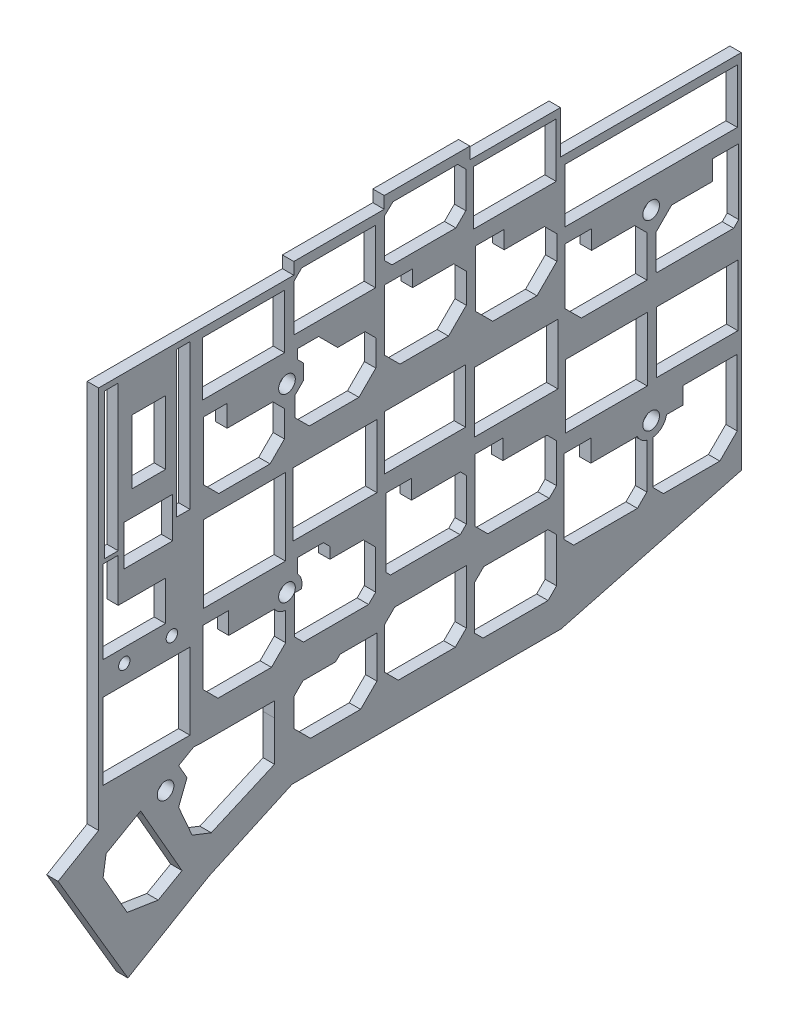
SolidWorks part; units mm, degrees
ref_plane "Спереди" through (0, 0, 0) normal (0, 0, 1) x (1, 0, 0)
ref_plane "Сверху" through (0, 0, 0) normal (0, 1, 0) x (1, 0, 0)
ref_plane "Справа" through (0, 0, 0) normal (1, 0, 0) x (0, 0, -1)
sketch "Эскиз1" plane through (0, 0, 0) normal (1, 0, 0) x (0, 0, -1)
  line L0 (0, 0) -> (0, -80.5)
  line L2 (41, 2.5) -> (41, 0)
  line L3 (41, 0) -> (0, 0)
  line L4 (41, 2.5) -> (60, 2.5)
  line L5 (60, 2.5) -> (60, 5)
  line L6 (41.1751, -59.6669) -> (41.1751, -57.8712)
  line L7 (41.1751, -57.8712) -> (42.5834, -57.8712)
  line L9 (78, 5) -> (78, 2.5)
  line L10 (78, 2.5) -> (97, 2.5)
  line L11 (97, 2.5) -> (97, -6.5)
  line L12 (97, -6.5) -> (135, -6.5)
  line L13 (135, -6.5) -> (135, -82.5)
  line L14 (135, -82.5) -> (97.1532, -92.4105)
  line L15 (97.1532, -92.4105) -> (40.6532, -92.4105)
  line L16 (40.6532, -92.4105) -> (23.1532, -100.4105)
  line L17 (23.1532, -100.4105) -> (6.1532, -110.4105)
  line L18 (6.1532, -110.4105) -> (-8.5, -85.5)
  line L19 (-8.5, -85.5) -> (0, -80.5)
  line L20 (115.2444, -43.8669) -> (98.0747, -43.8669)
  line L21 (134.2812, -43.8669) -> (117.1398, -43.8669)
  line L22 (134.2812, -43.8669) -> (134.2812, -56.7301)
  line L23 (134.2812, -56.7301) -> (117.1398, -56.7301)
  line L24 (117.1398, -43.8669) -> (117.1398, -56.7301)
  line L25 (134.2812, -43.8669) -> (117.1398, -56.7301) construction
  line L26 (134.2812, -56.7301) -> (117.1398, -43.8669) construction
  line L27 (115.2444, -43.8669) -> (115.2444, -57.2681)
  line L28 (115.2444, -57.2681) -> (98.0747, -57.2681)
  line L29 (98.0747, -43.8669) -> (98.0747, -57.2681)
  line L30 (96.4817, -35.7366) -> (78.9435, -35.7366)
  line L31 (96.4817, -35.7366) -> (96.4817, -48.4214)
  line L32 (96.4817, -48.4214) -> (78.9435, -48.4214)
  line L33 (78.9435, -35.7366) -> (78.9435, -48.4214)
  line L34 (77.0753, -34.3134) -> (60.0344, -34.3134)
  line L35 (77.0753, -34.3134) -> (77.0753, -45.6876)
  line L36 (77.0753, -45.6876) -> (60.0344, -45.6876)
  line L37 (60.0344, -34.3134) -> (60.0344, -45.6876)
  line L38 (39.2504, -34.986) -> (22.0882, -34.986)
  line L39 (39.2504, -34.986) -> (39.2504, -51.1261)
  line L40 (39.2504, -51.1261) -> (22.0882, -51.1261)
  line L41 (22.0882, -34.986) -> (22.0882, -51.1261)
  line L42 (58.4588, -34.9591) -> (40.7884, -34.9591)
  line L43 (58.4588, -34.9591) -> (58.4588, -48.279)
  line L44 (58.4588, -48.279) -> (40.7884, -48.279)
  line L45 (40.7884, -34.9591) -> (40.7884, -48.279)
  line L46 (39.085, -1.7522) -> (21.8397, -1.7522)
  line L47 (39.085, -1.7522) -> (39.085, -13.1264)
  line L48 (39.085, -13.1264) -> (21.8397, -13.1264)
  line L49 (21.8397, -1.7522) -> (21.8397, -13.1264)
  line L50 (114.4249, -8.3173) -> (97.9345, -8.3173)
  line L52 (115.1819, -19.6916) -> (97.9345, -19.6916)
  line L53 (97.9345, -8.3173) -> (97.9345, -19.6916)
  line L54 (75.4231, 2.9496) -> (61.8402, 2.9496)
  line L55 (77.1401, 1.2326) -> (77.1401, -6.3324)
  line L56 (75.0478, -8.4247) -> (61.6231, -8.4247)
  line L57 (60.0575, 1.2815) -> (60.0575, -6.8591)
  line L58 (58.1743, 0.5012) -> (42.6577, 0.5012)
  line L59 (58.1743, 0.5012) -> (58.1743, -10.8731)
  line L60 (58.1743, -10.8731) -> (41.0138, -10.8731)
  line L61 (41.0138, -1.1427) -> (41.0138, -10.8731)
  line L62 (134.1721, -8.3173) -> (114.4249, -8.3173)
  line L63 (134.1721, -8.3173) -> (134.1721, -19.6916)
  line L64 (134.1721, -19.6916) -> (115.1819, -19.6916)
  line L66 (96.1243, 0.8798) -> (78.7359, 0.8798)
  line L67 (96.1243, 0.8798) -> (96.1243, -10.4945)
  line L68 (96.1243, -10.4945) -> (78.7359, -10.4945)
  line L69 (78.7359, 0.8798) -> (78.7359, -10.4945)
  line L70 (61.8402, 2.9496) -> (60.0575, 1.2815)
  line L71 (78, 5) -> (60, 5)
  line L72 (75.4231, 2.9496) -> (77.1401, 1.2326)
  line L73 (77.1401, -6.3324) -> (75.0478, -8.4247)
  line L74 (60.0575, -6.8591) -> (61.6231, -8.4247)
  line L75 (42.6577, 0.5012) -> (41.0138, -1.1427)
  line L76 (134.4455, -22.7884) -> (134.4455, -36.6029)
  line L81 (19.1956, -1.1776) -> (16.3872, -1.1776)
  line L82 (19.1956, -1.1776) -> (19.1956, -31.6801)
  line L83 (19.1956, -31.6801) -> (16.3872, -31.6801)
  line L84 (16.3872, -1.1776) -> (16.3872, -31.6801)
  line L85 (14.07, -8.4247) -> (7.0177, -8.4247)
  line L86 (14.07, -8.4247) -> (14.07, -21.8565)
  line L87 (14.07, -21.8565) -> (7.0177, -21.8565)
  line L88 (7.0177, -8.4247) -> (7.0177, -21.8565)
  line L89 (4.123, -1.1776) -> (1.2335, -1.1776)
  line L90 (4.123, -1.1776) -> (4.123, -31.6801)
  line L91 (4.123, -31.6801) -> (1.2335, -31.6801)
  line L92 (1.2335, -1.1776) -> (1.2335, -31.6801)
  line L93 (15.5712, -27.119) -> (5.2984, -27.119)
  line L94 (15.5712, -27.119) -> (15.5712, -35.5999)
  line L95 (15.5712, -35.5999) -> (5.2984, -35.5999)
  line L96 (5.2984, -27.119) -> (5.2984, -35.5999)
  line L97 (4.123, -32.4925) -> (0.9179, -32.4925)
  line L98 (4.123, -32.4925) -> (4.123, -41.6217)
  line L100 (0.9179, -32.4925) -> (0.9179, -49.8922)
  line L105 (134.4455, -36.6029) -> (133.3973, -37.6511)
  line L106 (133.3973, -37.6511) -> (117.3195, -37.6511)
  line L107 (117.3195, -37.6511) -> (117.0331, -37.3648)
  line L108 (117.0331, -37.3648) -> (117.0331, -30.2531)
  line L109 (117.0331, -30.2531) -> (120.3714, -26.9148)
  line L110 (120.3714, -26.9148) -> (128.9098, -26.9148)
  line L111 (128.9098, -26.9148) -> (128.9098, -22.7884)
  line L112 (128.9098, -22.7884) -> (134.4455, -22.7884)
  line L113 (97.9345, -22.7884) -> (97.9345, -34.5253)
  line L114 (97.9345, -34.5253) -> (101.3903, -37.9811)
  line L115 (101.3903, -37.9811) -> (115.1819, -37.9811)
  line L116 (115.1819, -37.9811) -> (115.1819, -29.341)
  line L117 (115.1819, -29.341) -> (112.6062, -26.7653)
  line L118 (112.6062, -26.7653) -> (103.5391, -26.7653)
  line L119 (103.5391, -26.7653) -> (103.5391, -22.7884)
  line L120 (103.5391, -22.7884) -> (97.9345, -22.7884)
  line L121 (79.1801, -13.7463) -> (79.1801, -25.658)
  line L122 (79.1801, -25.658) -> (82.7928, -29.2707)
  line L123 (82.7928, -29.2707) -> (92.0789, -29.2707)
  line L124 (92.0789, -29.2707) -> (96.2546, -25.095)
  line L125 (96.2546, -25.095) -> (96.2546, -20.0763)
  line L126 (96.2546, -20.0763) -> (93.6526, -17.4743)
  line L127 (93.6526, -17.4743) -> (85.1909, -17.4743)
  line L128 (85.1909, -17.4743) -> (85.1909, -13.7463)
  line L129 (85.1909, -13.7463) -> (79.1801, -13.7463)
  line L130 (60.0575, -11.5433) -> (60.0575, -24.0649)
  line L131 (60.0575, -24.0649) -> (63.3126, -27.32)
  line L132 (63.3126, -27.32) -> (73.507, -27.32)
  line L133 (73.507, -27.32) -> (77.2434, -23.5835)
  line L134 (77.2434, -23.5835) -> (77.2434, -17.384)
  line L135 (77.2434, -17.384) -> (74.5983, -14.7389)
  line L136 (74.5983, -14.7389) -> (65.9509, -14.7389)
  line L137 (65.9509, -14.7389) -> (65.9509, -11.2966)
  line L138 (65.9509, -11.2966) -> (60.0575, -11.2966)
  line L139 (60.0575, -11.2966) -> (60.0575, -11.5433)
  line L140 (41.2039, -21.9909) -> (41.2039, -25.9973)
  line L141 (41.2039, -25.9973) -> (44.2553, -29.0487)
  line L142 (44.2553, -29.0487) -> (54.6792, -29.0487)
  line L143 (54.6792, -29.0487) -> (58.222, -25.506)
  line L144 (58.222, -25.506) -> (58.222, -19.9911)
  line L145 (58.222, -19.9911) -> (55.979, -17.7482)
  line L146 (55.979, -17.7482) -> (50.2068, -17.7482)
  line L147 (50.2068, -17.7482) -> (46.2049, -13.7463)
  line L148 (46.2049, -13.7463) -> (41.7463, -13.7463)
  line L149 (41.7463, -13.7463) -> (41.7463, -15.6937)
  line L150 (41.7463, -15.6937) -> (43.0018, -16.9493)
  line L151 (43.0018, -16.9493) -> (43.0018, -20.193)
  line L152 (43.0018, -20.193) -> (41.2039, -21.9909)
  line L153 (22.0882, -16.2929) -> (22.0882, -28.227)
  line L154 (22.0882, -16.2929) -> (27.0021, -16.2929)
  line L155 (27.0021, -16.2929) -> (27.0021, -20.8389)
  line L156 (27.0021, -20.8389) -> (36.6084, -20.8389)
  line L157 (36.6084, -20.8389) -> (39.04, -23.2705)
  line L158 (39.04, -23.2705) -> (39.04, -28.8092)
  line L159 (39.04, -28.8092) -> (36.0163, -31.8329)
  line L160 (36.0163, -31.8329) -> (25.2427, -31.8329)
  line L161 (25.2427, -31.8329) -> (22.0882, -28.6784)
  line L162 (22.0882, -28.6784) -> (22.0882, -28.227)
  line L163 (134.1429, -60.9376) -> (134.1429, -74.9003)
  line L164 (134.1429, -74.9003) -> (130.4912, -78.552)
  line L165 (130.4912, -78.552) -> (118.6526, -78.552)
  line L166 (118.6526, -78.552) -> (116.4367, -76.3361)
  line L167 (116.4367, -76.3361) -> (116.4367, -67.1958)
  line L169 (119.2828, -64.5018) -> (122.7046, -64.5018)
  line L170 (122.7046, -64.5018) -> (122.7046, -60.9376)
  line L171 (122.7046, -60.9376) -> (134.1429, -60.9376)
  line L172 (115.1516, -67.0844) -> (115.1516, -76.5165)
  line L173 (115.1516, -76.5165) -> (113.175, -78.4931)
  line L174 (113.175, -78.4931) -> (99.8049, -78.4931)
  line L175 (99.8049, -78.4931) -> (97.7485, -76.4366)
  line L176 (97.7485, -76.4366) -> (97.7485, -60.8193)
  line L177 (97.7485, -60.8193) -> (103.3958, -60.8193)
  line L178 (103.3958, -60.8193) -> (103.3958, -65.3906)
  line L179 (103.3958, -65.3906) -> (113.1434, -65.3906)
  line L181 (94.3901, -72.9633) -> (96.1915, -74.7647)
  line L182 (96.1915, -74.7647) -> (96.1915, -84.0984)
  line L183 (96.1915, -84.0984) -> (94.4093, -85.8807)
  line L184 (94.4093, -85.8807) -> (80.7614, -85.8807)
  line L185 (80.7614, -85.8807) -> (78.9435, -84.0628)
  line L186 (78.9435, -84.0628) -> (78.9435, -74.9072)
  line L187 (78.9435, -74.9072) -> (80.9028, -72.9479)
  line L188 (80.9028, -72.9479) -> (89.3287, -72.9479)
  line L189 (89.3287, -72.9479) -> (89.3072, -72.9633)
  line L190 (89.3072, -72.9633) -> (92.0789, -72.9633)
  line L191 (92.0789, -72.9633) -> (94.3901, -72.9633)
  line L192 (96.1915, -57.6954) -> (96.1915, -63.958)
  line L193 (96.1915, -57.6954) -> (94.18, -55.6839)
  line L194 (94.18, -55.6839) -> (84.911, -55.6839)
  line L195 (84.911, -55.6839) -> (84.911, -51.5792)
  line L196 (84.911, -51.5792) -> (79.0384, -51.5792)
  line L197 (79.0384, -51.5792) -> (79.0384, -64.6854)
  line L198 (79.0384, -64.6854) -> (81.7682, -67.4152)
  line L199 (81.7682, -67.4152) -> (94.6543, -67.4152)
  line L200 (94.6543, -67.4152) -> (96.1915, -65.878)
  line L201 (96.1915, -65.878) -> (96.1915, -63.958)
  line L202 (60.3332, -49.2925) -> (60.3332, -63.7083)
  line L203 (60.3332, -63.7083) -> (61.3103, -64.6854)
  line L204 (61.3103, -64.6854) -> (75.9502, -64.6854)
  line L205 (75.9502, -64.6854) -> (77.2397, -63.3959)
  line L206 (77.2397, -63.3959) -> (77.2397, -54.5235)
  line L207 (77.2397, -54.5235) -> (76.006, -53.2898)
  line L208 (76.006, -53.2898) -> (65.7297, -53.2898)
  line L209 (65.7297, -53.2898) -> (65.7297, -49.2925)
  line L210 (65.7297, -49.2925) -> (60.3332, -49.2925)
  line L211 (77.2397, -70.92) -> (77.2397, -82.3079)
  line L212 (77.2397, -82.3079) -> (74.9117, -84.6359)
  line L213 (74.9117, -84.6359) -> (62.9489, -84.6359)
  line L214 (62.9489, -84.6359) -> (60.0344, -81.7213)
  line L215 (60.0344, -81.7213) -> (60.0344, -73.1228)
  line L216 (60.0344, -73.1228) -> (62.1913, -70.966)
  line L217 (62.1913, -70.966) -> (69.6708, -70.966)
  line L218 (69.6708, -70.966) -> (69.6708, -70.92)
  line L219 (69.6708, -70.92) -> (77.2397, -70.92)
  line L220 (58.4588, -74.1904) -> (58.4588, -82.5614)
  line L221 (58.4588, -82.5614) -> (55.0335, -85.9867)
  line L222 (55.0335, -85.9867) -> (44.5165, -85.9867)
  line L223 (44.5165, -85.9867) -> (41.0138, -82.484)
  line L224 (41.0138, -82.484) -> (41.0138, -76.6283)
  line L225 (41.0138, -76.6283) -> (42.929, -74.7131)
  line L226 (42.929, -74.7131) -> (49.7913, -74.7131)
  line L227 (49.7913, -74.7131) -> (50.7049, -73.7995)
  line L228 (50.7049, -73.7995) -> (58.4588, -73.7995)
  line L229 (58.4588, -73.7995) -> (58.4588, -74.1904)
  line L230 (41.7463, -51.7434) -> (41.7463, -54.6825)
  line L234 (41.1751, -59.6669) -> (41.1751, -65.8913)
  line L235 (41.1751, -65.8913) -> (43.0301, -67.7463)
  line L236 (43.0301, -67.7463) -> (56.7142, -67.7463)
  line L237 (56.7142, -67.7463) -> (58.2067, -66.2538)
  line L238 (58.2067, -66.2538) -> (58.2067, -58.0562)
  line L239 (58.2067, -58.0562) -> (55.6211, -55.4707)
  line L240 (55.6211, -55.4707) -> (48.5878, -55.4707)
  line L241 (48.5878, -55.4707) -> (48.5878, -53.1196)
  line L242 (48.5878, -53.1196) -> (47.2116, -51.7434)
  line L243 (47.2116, -51.7434) -> (41.7463, -51.7434)
  line L244 (27.335, -54.1406) -> (27.335, -58.6932)
  line L245 (27.335, -58.6932) -> (36.9426, -58.6932)
  line L247 (39.2975, -60.0949) -> (39.2975, -65.9987)
  line L248 (39.2975, -65.9987) -> (36.3132, -68.9829)
  line L249 (36.3132, -68.9829) -> (25.0829, -68.9829)
  line L250 (25.0829, -68.9829) -> (21.9132, -65.8133)
  line L251 (21.9132, -65.8133) -> (21.9132, -54.1406)
  line L252 (21.9132, -54.1406) -> (27.335, -54.1406)
  line L253 (19.1956, -56.7301) -> (19.1956, -72.7671)
  line L254 (19.1956, -72.7671) -> (0.9179, -72.7671)
  line L255 (0.9179, -72.7671) -> (0.9179, -56.7301)
  line L256 (0.9179, -56.7301) -> (19.1956, -56.7301)
  line L258 (0.9179, -49.8922) -> (14.07, -49.8922)
  line L259 (14.07, -49.8922) -> (14.07, -41.6217)
  line L260 (14.07, -41.6217) -> (4.123, -41.6217)
  line L261 (36.9426, -75.3779) -> (36.9426, -78.5072)
  line L262 (36.9426, -78.5072) -> (36.9492, -78.5005)
  line L263 (36.9492, -78.5005) -> (36.9492, -86.9326)
  line L264 (36.9492, -86.9326) -> (23.6687, -92.7489)
  line L265 (23.6687, -92.7489) -> (19.6493, -91.1779)
  line L266 (19.6493, -91.1779) -> (16.8062, -84.6861)
  line L267 (16.8062, -84.6861) -> (18.5715, -80.1697)
  line L268 (18.5715, -80.1697) -> (16.818, -77.1037)
  line L269 (16.818, -77.1037) -> (19.9877, -75.2908)
  line L270 (36.9426, -75.3779) -> (21.3449, -75.3779)
  line L274 (9.4762, -82.4846) -> (17.528, -96.563)
  line L275 (17.528, -96.563) -> (12.5276, -99.4228)
  line L276 (12.5276, -99.4228) -> (6, -98.3963)
  line L277 (6, -98.3963) -> (0.9484, -89.5637)
  line L278 (0.9484, -89.5637) -> (1.5875, -85.5)
  line L279 (1.5875, -85.5) -> (8.8323, -81.3565)
  line L280 (8.8323, -81.3565) -> (9.4762, -82.4846)
  line L285 (19.9877, -75.2908) -> (21.3449, -75.3779)
  circle A0 centre (39.57, -56.958) radius 1.75
  circle A1 centre (116.07, -63.958) radius 1.75
  circle A2 centre (116.07, -25.658) radius 1.75
  circle A3 centre (39.57, -19.048) radius 1.75
  circle A5 centre (15.3897, -52.7834) radius 1.1956
  circle A6 centre (5.3984, -52.8076) radius 1.1956
  circle A7 centre (14.07, -80.258) radius 1.75
  arc A8 (116.4367, -67.1958) -> (119.2828, -64.5018) centre (116.07, -63.958) ccw
  arc A9 (113.1434, -65.3906) -> (115.1516, -67.0844) centre (116.07, -63.958) ccw
  arc A10 (42.5834, -57.8712) -> (41.7463, -54.6825) centre (39.57, -56.958) ccw
  arc A11 (36.9426, -58.6932) -> (39.2975, -60.0949) centre (39.57, -56.958) ccw
  point P8 (27.3605, -36.9806)
  point P9 (22.2159, -36.0538)
  point P53 (125.7105, -50.2985)
  dimension "D1" = 3.5
  dimension "D2" = 76.5
  dimension "D3" = 38.3
  dimension "D4" = 37.91
  dimension "D5" = 19.048
  dimension "D6" = 39.57
  dimension "D7" = 80.258
  dimension "D8" = 14.07
  dimension "D9" = 80.5
  dimension "D10" = 135
  dimension "D11" = 38
  dimension "D12" = 19
  dimension "D13" = 18
  dimension "D14" = 19
  dimension "D15" = 9
  dimension "D16" = 2.5
  dimension "D17" = 2.5
  dimension "D18" = 9.8615
  dimension "D19" = 28.9007
  dimension "D20" = 120.466
  dimension "D21" = 75.326
  dimension "D22" = 39.1228
  dimension "D23" = 56.5
  dimension "D24" = 19.7231
  dimension "D25" = 24.567
extrude "Бобышка-Вытянуть1" add sketch "Эскиз1" along normal blind 2.4
